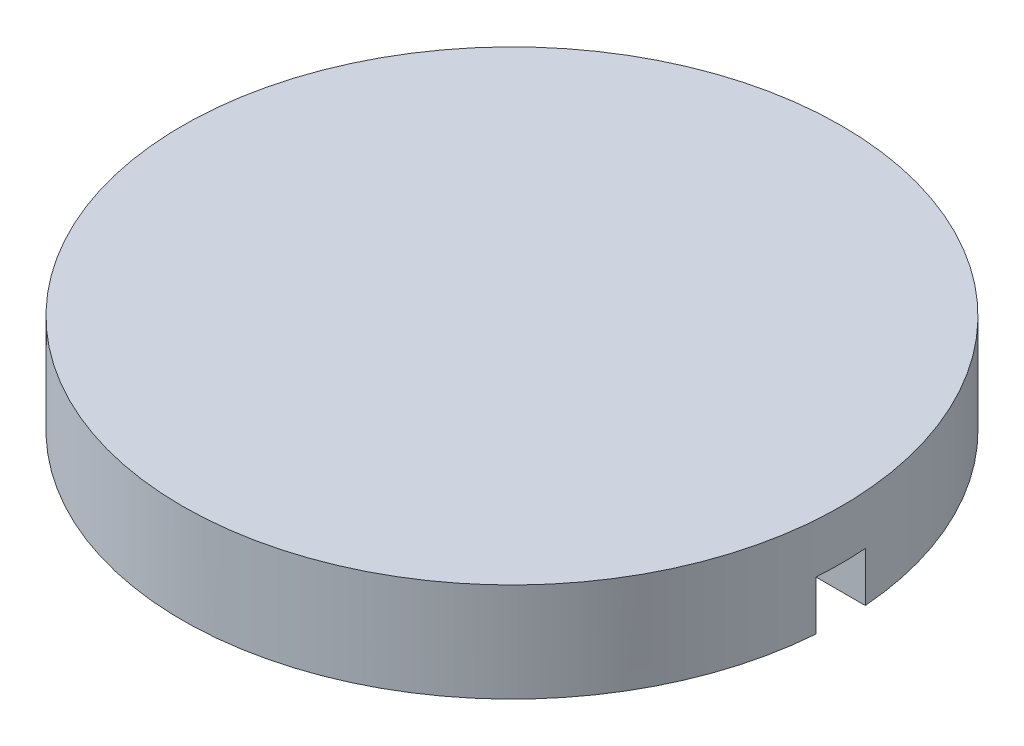
SolidWorks part; units mm, degrees
ref_plane "Plano frontal" through (0, 0, 0) normal (0, 0, 1) x (1, 0, 0)
ref_plane "Plano superior" through (0, 0, 0) normal (0, 1, 0) x (1, 0, 0)
ref_plane "Plano direito" through (0, 0, 0) normal (1, 0, 0) x (0, 0, -1)
sketch "Esboço1" plane through (0, 0, 0) normal (0, 0, 1) x (1, 0, 0)
  line L0 (0, 0) -> (0, 302.0341) construction
  line L1 (0, 0) -> (300.8169, 0) construction
  line L2 (0, 60) -> (200, 60)
  line L3 (200, 60) -> (200, 0)
  line L4 (200, 0) -> (0, 0)
  line L5 (0, 0) -> (0, 60)
  dimension "D1" = 400
  dimension "D2" = 60
revolve "Revolução1" add sketch "Esboço1" angle 360 about L0
sketch "Esboço2" plane through (0, 0, 0) normal (1, 0, 0) x (0, 0, -1)
  line L0 (-200, 0) -> (200, 0) construction
  line L1 (-15, 0) -> (15, 0)
  line L2 (-15, 0) -> (-15, 30)
  line L3 (-15, 30) -> (15, 30)
  line L4 (15, 0) -> (15, 30)
  point P6 (0, 0)
  dimension "D1" = 30
  dimension "D2" = 30
extrude "Corte-extrusão1" cut sketch "Esboço2" against normal through all both and the other way through all
